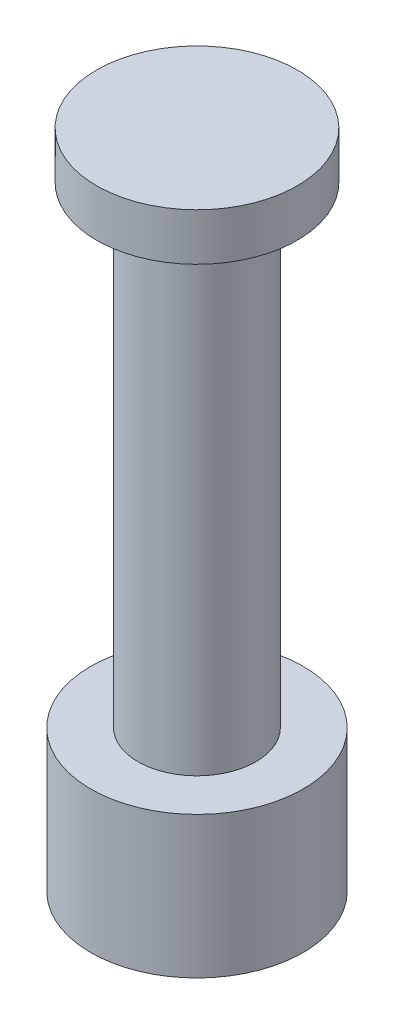
SolidWorks part; units mm, degrees
ref_plane "Front" through (0, 0, 0) normal (0, 0, 1) x (1, 0, 0)
ref_plane "Top" through (0, 0, 0) normal (0, 1, 0) x (1, 0, 0)
ref_plane "Right" through (0, 0, 0) normal (1, 0, 0) x (0, 0, -1)
sketch "Sketch1" plane through (0, 0, 0) normal (0, 0, 1) x (1, 0, 0)
  line L0 (0, 14) -> (4.25, 14)
  line L1 (4.25, 14) -> (4.25, 12)
  line L2 (4.25, 12) -> (2.5, 12)
  line L3 (2.5, 12) -> (2.5, -8)
  line L4 (2.5, -8) -> (4.5, -8)
  line L5 (4.5, -8) -> (4.5, -14)
  line L6 (4.5, -14) -> (0, -14)
  line L7 (0, 14) -> (0, -14)
  point P7 (0, 0)
  dimension "D1" = 2
  dimension "D2" = 26
  dimension "D3" = 6
  dimension "D4" = 4.25
  dimension "D5" = 2.5
  dimension "D6" = 4.5
revolve "Revolve1" add sketch "Sketch1" angle 360 about L7
